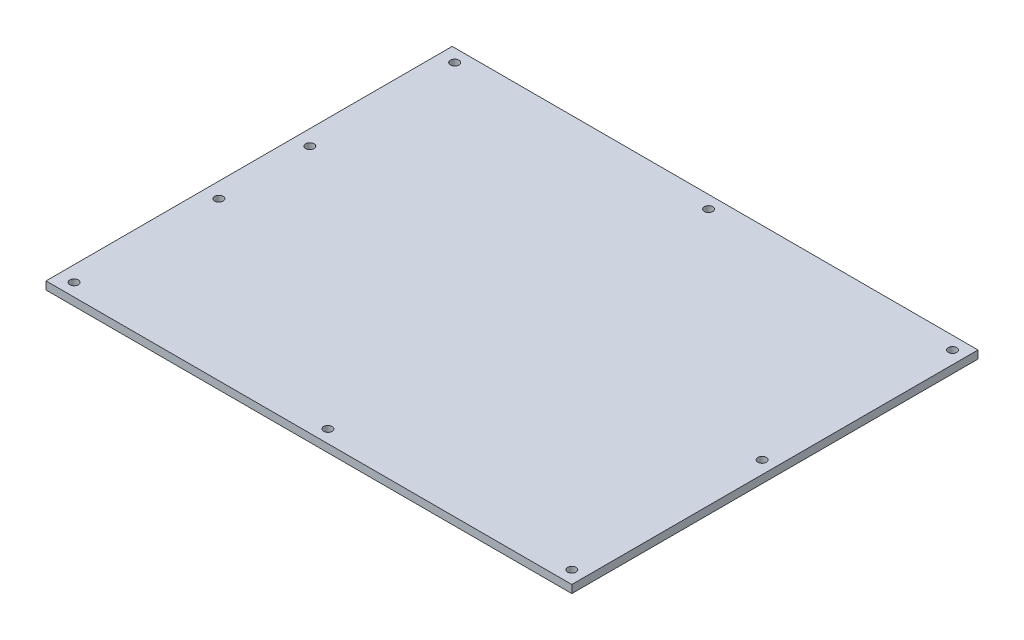
SolidWorks part; units mm, degrees
ref_plane "Front Plane" through (0, 0, 0) normal (0, 0, 1) x (1, 0, 0)
ref_plane "Top Plane" through (0, 0, 0) normal (0, 1, 0) x (1, 0, 0)
ref_plane "Right Plane" through (0, 0, 0) normal (1, 0, 0) x (0, 0, -1)
sketch "Sketch1" plane through (0, 0, 0) normal (0, 1, 0) x (1, 0, 0)
  line L8 (-105.5, 0) -> (105.5, 0) construction
  line L9 (-105.5, -81.5) -> (105.5, -81.5)
  line L14 (-105.5, -81.5) -> (-105.5, 81.5)
  line L15 (-105.5, 81.5) -> (105.5, 81.5)
  line L16 (105.5, -81.5) -> (105.5, 81.5)
  line L17 (-105.5, -81.5) -> (105.5, 81.5) construction
  line L18 (-105.5, 81.5) -> (105.5, -81.5) construction
  point P0 (0, 0)
  dimension "D1" = 211
  dimension "D2" = 163
extrude "Boss-Extrude1" add sketch "Sketch1" along normal blind 3.175
sketch "Sketch2" plane through (0, 0, 0) normal (0, -1, 0) x (-1, 0, 0)
  circle A1 centre (99.375, -76.375) radius 1.7
  circle A2 centre (-2.5, -76.375) radius 1.7
  circle A3 centre (-100.375, -76.375) radius 1.7
  circle A4 centre (-100.375, 0) radius 1.7
  circle A5 centre (-100.375, 76.375) radius 1.7
  circle A6 centre (-2.5, 76.375) radius 1.7
  circle A7 centre (99.375, 76.375) radius 1.7
  circle A8 centre (99.375, 18.25) radius 1.7
  circle A9 centre (99.375, -18.25) radius 1.7
  circle A10 centre (99.375, -76.375) radius 1.7 construction
  circle A11 centre (99.375, -18.25) radius 1.7 construction
  circle A12 centre (99.375, 18.25) radius 1.7 construction
  circle A13 centre (99.375, 76.375) radius 1.7 construction
  circle A14 centre (-2.5, 76.375) radius 1.7 construction
  circle A15 centre (-100.375, 76.375) radius 1.7 construction
  circle A16 centre (-100.375, 0) radius 1.7 construction
  circle A17 centre (-100.375, -76.375) radius 1.7 construction
  circle A18 centre (-2.5, -76.375) radius 1.7 construction
  point P2 (99.7448, -71.2882)
  point P9 (0, 0)
  point P24 (0, 0)
  point P29 (0, 0)
  point P32 (0, 0)
  point P35 (0, 0)
  point P38 (0, 0)
  point P41 (0, 0)
  dimension "D1" = 3.4
extrude "Cut-Extrude1" cut sketch "Sketch2" against normal through all
